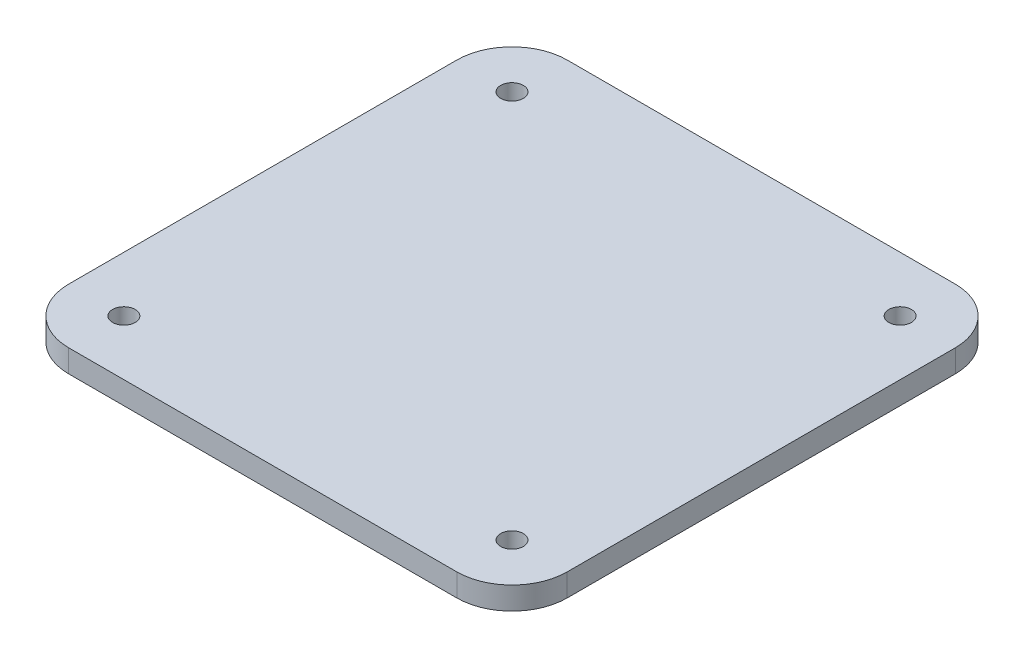
SolidWorks part; units mm, degrees
material "Pino"
ref_plane "Alzado" through (0, 0, 0) normal (0, 0, 1) x (1, 0, 0)
ref_plane "Planta" through (0, 0, 0) normal (0, 1, 0) x (1, 0, 0)
ref_plane "Vista lateral" through (0, 0, 0) normal (1, 0, 0) x (0, 0, -1)
sketch "Croquis1" plane through (0, 0, 0) normal (0, 1, 0) x (1, 0, 0)
  line L1 (-109, -140) -> (109, -140)
  line L2 (-140, -109) -> (-140, 109)
  line L3 (-109, 140) -> (109, 140)
  line L4 (140, -109) -> (140, 109)
  line L5 (-140, -140) -> (140, 140) construction
  line L6 (-140, 140) -> (140, -140) construction
  arc A0 (-109, -140) -> (-140, -109) centre (-109, -109) cw
  arc A1 (109, -140) -> (140, -109) centre (109, -109) ccw
  arc A2 (109, 140) -> (140, 109) centre (109, 109) cw
  arc A3 (-140, 109) -> (-109, 140) centre (-109, 109) cw
  point P0 (0, 0)
  dimension "D3" = 31
  dimension "D1" = 280
  dimension "D2" = 280
extrude "Saliente-Extruir1" add sketch "Croquis1" along normal blind 12.7
sketch "Croquis2" plane through (0, 12.7, 0) normal (0, 1, 0) x (1, 0, 0)
  line L0 (140, -109) -> (140, 109) construction
  line L1 (109, 140) -> (-109, 140) construction
  line L2 (-109, -140) -> (109, -140) construction
  circle A0 centre (109, 109) radius 6.35
  circle A1 centre (109, -109) radius 6.35
  circle A2 centre (-109, -109) radius 6.35
  circle A3 centre (-109, 109) radius 6.35
  point P15 (0, 0)
  dimension "D3" = 12.7
  dimension "D1" = 31
  dimension "D2" = 31
  dimension "D5" = 31
  dimension "D4" = 4
extrude "Cortar-Extruir1" cut sketch "Croquis2" against normal through all
